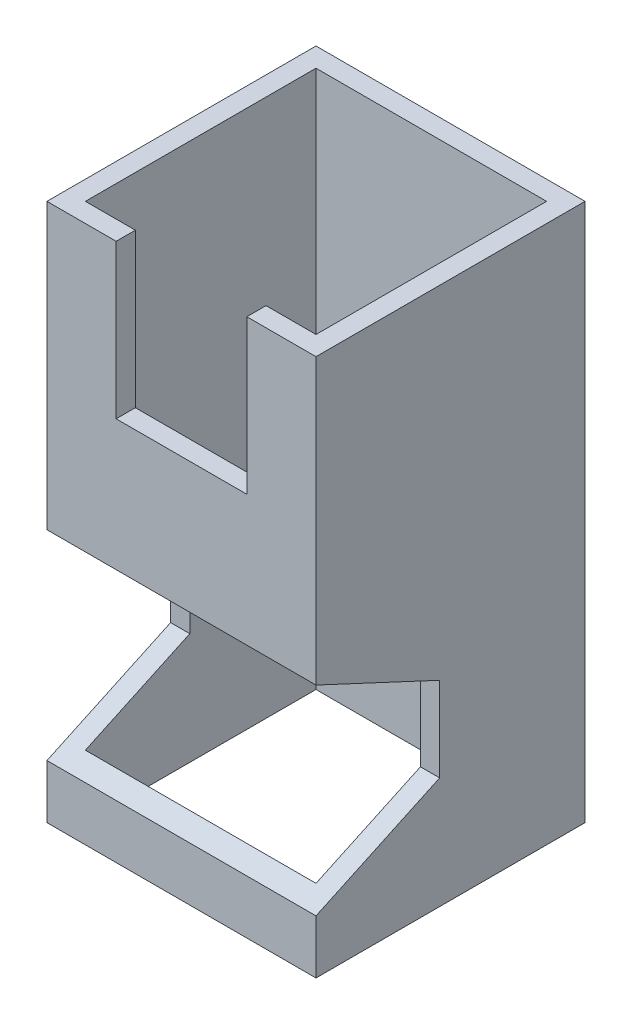
SolidWorks part; units mm, degrees
ref_plane "Front Plane" through (0, 0, 0) normal (0, 0, 1) x (1, 0, 0)
ref_plane "Top Plane" through (0, 0, 0) normal (0, 1, 0) x (1, 0, 0)
ref_plane "Right Plane" through (0, 0, 0) normal (1, 0, 0) x (0, 0, -1)
sketch "Sketch1" plane through (0, 0, 0) normal (0, 1, 0) x (1, 0, 0)
  line L1 (0, 0) -> (30, 0)
  line L2 (0, 0) -> (0, 30)
  line L3 (0, 30) -> (30, 30)
  line L4 (30, 0) -> (30, 30)
  line L5 (0, 0) -> (30, 30) construction
  line L6 (0, 30) -> (30, 0) construction
  line L7 (-2.5, 32.5) -> (32.5, 32.5)
  line L8 (-2.5, 32.5) -> (-2.5, -2.5)
  line L9 (-2.5, -2.5) -> (32.5, -2.5)
  line L10 (32.5, 32.5) -> (32.5, -2.5)
  line L11 (-2.5, 32.5) -> (32.5, -2.5) construction
  line L12 (-2.5, -2.5) -> (32.5, 32.5) construction
  point P4 (15, 15)
  point P10 (15, 15)
  dimension "D1" = 2.5
  dimension "D2" = 30
extrude "Boss-Extrude1" add sketch "Sketch1" along normal blind 70
sketch "Sketch2" plane through (0, 0, 2.5) normal (0, 0, 1) x (1, 0, 0)
  line L0 (-2.5, 70) -> (32.5, 70) construction
  line L1 (6.5, 70) -> (23.5, 70)
  line L2 (6.5, 70) -> (6.5, 50)
  line L3 (6.5, 50) -> (23.5, 50)
  line L4 (23.5, 70) -> (23.5, 50)
  line L5 (6.5, 70) -> (23.5, 50) construction
  line L6 (6.5, 50) -> (23.5, 70) construction
  line L7 (15, 0) -> (15, 60) construction
  line L8 (-2.5, 0) -> (32.5, 0) construction
  line L9 (15, 60) -> (15, 70) construction
  point P4 (15, 60)
  dimension "D1" = 20
  dimension "D2" = 17
extrude "Cut-Extrude1" cut sketch "Sketch2" against normal up to surface (2.5 mm away) up to face at (15, 35, 0)
sketch "Sketch3" plane through (-2.5, 0, 0) normal (-1, 0, 0) x (0, 0, 1)
  line L0 (2.5, 33) -> (-13.5838, 25.5)
  line L1 (2.5, 70) -> (2.5, 0) construction
  line L2 (-13.5838, 25.5) -> (-13.5838, 14.5)
  line L3 (-13.5838, 14.5) -> (2.5, 7)
  line L4 (2.5, 7) -> (2.5, 33)
  line L5 (-13.5838, 20) -> (2.5, 20) construction
  line L6 (-13.5838, 14.5) -> (-25.3786, 20) construction
  line L7 (-25.3786, 20) -> (-13.5838, 25.5) construction
  line L8 (-32.5, 0) -> (2.5, 0) construction
  dimension "D1" = 50
  dimension "D2" = 26
  dimension "D3" = 11
  dimension "D4" = 20
extrude "Cut-Extrude2" cut sketch "Sketch3" against normal through all
